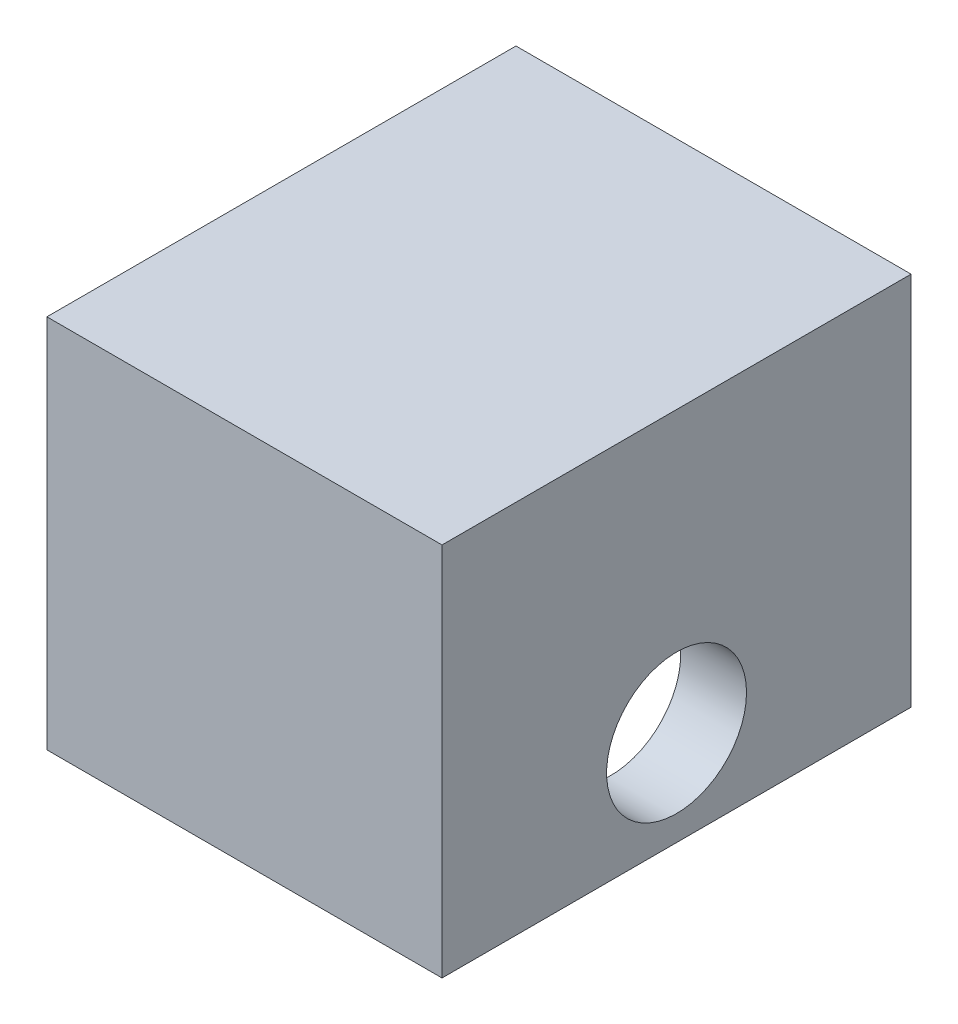
SolidWorks part; units mm, degrees
ref_plane "Front Plane" through (0, 0, 0) normal (0, 0, 1) x (1, 0, 0)
ref_plane "Top Plane" through (0, 0, 0) normal (0, 1, 0) x (1, 0, 0)
ref_plane "Right Plane" through (0, 0, 0) normal (1, 0, 0) x (0, 0, -1)
sketch "Sketch1" plane through (0, 0, 0) normal (0, 0, 1) x (1, 0, 0)
  line L0 (0, 0) -> (0, 10.0889)
  line L1 (0, 10.0889) -> (8.001, 10.0889)
  line L2 (8.001, 10.0889) -> (8.001, 0)
  line L3 (8.001, 0) -> (10, 0)
  line L6 (10, 0) -> (10, 12.0879)
  line L7 (10, 12.0879) -> (-1.999, 12.0879)
  line L8 (-1.999, 12.0879) -> (-1.999, 0)
  line L9 (-1.999, 0) -> (0, 0)
  dimension "D1" = 10.0889
  dimension "D2" = 8.001
  dimension "D3" = 1.999
extrude "Boss-Extrude1" add sketch "Sketch1" along normal blind 10.2464
sketch "Sketch2" plane through (10, 0, 0) normal (1, 0, 0) x (0, 0, -1)
  circle A0 centre (-5.1232, 3.5865) radius 2.1247
  dimension "D2" = 4.2494
extrude "Cut-Extrude1" cut sketch "Sketch2" against normal through all
sketch "Sketch3" plane through (10, 0, 0) normal (1, 0, 0) x (0, 0, -1)
  line L0 (-10.2464, 0) -> (-10.2464, 0.6985)
  line L1 (-10.2464, 0) -> (-10.2464, 12.0879) construction
  line L2 (-10.2464, 0.6985) -> (0, 0.6985)
  line L3 (0, 0) -> (0, 12.0879) construction
  line L4 (0, 0.6985) -> (0, 0)
  line L5 (0, 0) -> (-10.2464, 0)
  dimension "D1" = 0.6985
extrude "Cut-Extrude2" cut sketch "Sketch3" against normal through all
sketch "Sketch4" plane through (10, 0, 0) normal (1, 0, 0) x (0, 0, -1)
  line L0 (-10.2464, 12.0879) -> (-12.2453, 12.0879)
  line L1 (-12.2453, 12.0879) -> (-12.2453, 0.6985)
  line L2 (-12.2453, 0.6985) -> (-10.2464, 0.6985)
  line L3 (-10.2464, 0.6985) -> (-10.2464, 12.0879)
  line L4 (0, 12.0879) -> (1.999, 12.0879)
  line L5 (1.999, 12.0879) -> (1.999, 0.6985)
  line L6 (1.999, 0.6985) -> (0, 0.6985)
  line L7 (0, 12.0879) -> (0, 0.6985)
  dimension "D1" = 1.999
  dimension "D2" = 1.999
extrude "Boss-Extrude2" add sketch "Sketch4" against normal blind 11.999
